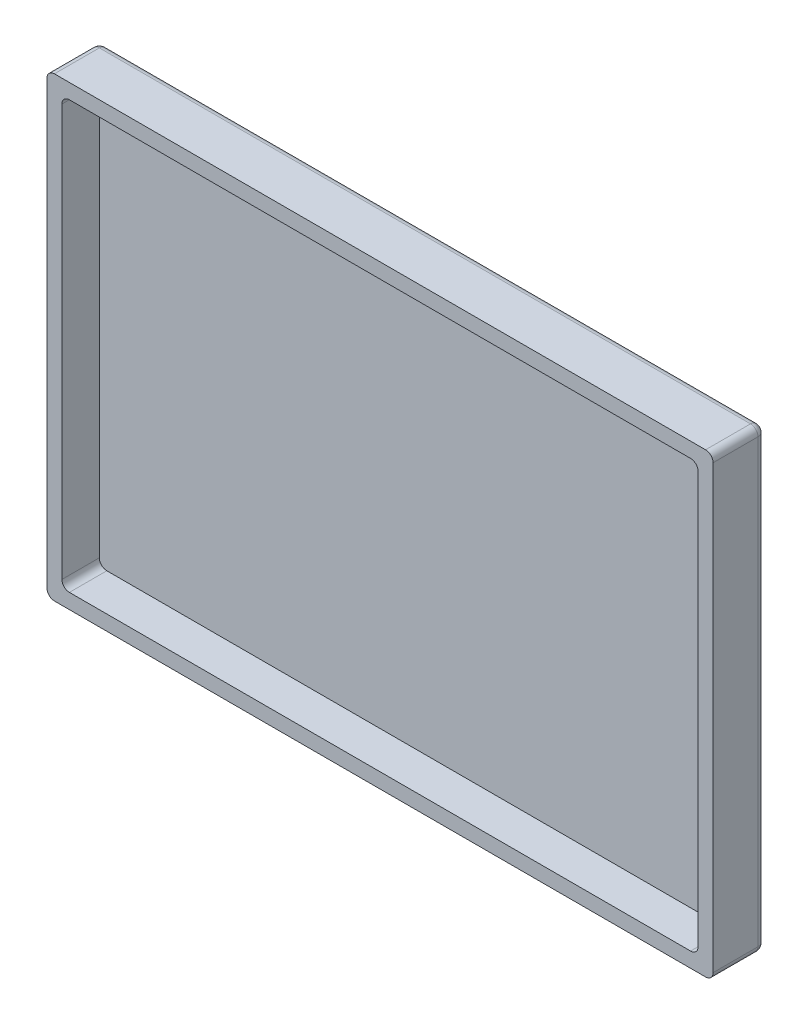
SolidWorks part; units mm, degrees
ref_plane "Plano frontal" through (0, 0, 0) normal (0, 0, 1) x (1, 0, 0)
ref_plane "Plano superior" through (0, 0, 0) normal (0, 1, 0) x (1, 0, 0)
ref_plane "Plano direito" through (0, 0, 0) normal (1, 0, 0) x (0, 0, -1)
sketch "Esboço1" plane through (0, 0, 0) normal (0, 0, 1) x (1, 0, 0)
  line L1 (-44.7633, 12.2986) -> (40.2367, 12.2986)
  line L2 (-44.7633, 12.2986) -> (-44.7633, -44.7014)
  line L3 (-44.7633, -44.7014) -> (40.2367, -44.7014)
  line L4 (40.2367, 12.2986) -> (40.2367, -44.7014)
  line L5 (-46.7633, 14.2986) -> (42.2367, 14.2986)
  line L6 (-46.7633, 14.2986) -> (-46.7633, -46.7014)
  line L7 (-46.7633, -46.7014) -> (42.2367, -46.7014)
  line L8 (42.2367, 14.2986) -> (42.2367, -46.7014)
  dimension "D1" = 57
  dimension "D2" = 85
  dimension "D3" = 2
  dimension "D4" = 2
  dimension "D5" = 2
  dimension "D6" = 2
extrude "Ressalto-extrusão1" add sketch "Esboço1" along normal blind 5
sketch "Esboço2" plane through (0, 0, 0) normal (0, 0, -1) x (-1, 0, 0)
  line L1 (-42.2367, 14.2986) -> (46.7633, 14.2986)
  line L2 (-42.2367, 14.2986) -> (-42.2367, -46.7014)
  line L3 (-42.2367, -46.7014) -> (46.7633, -46.7014)
  line L4 (46.7633, 14.2986) -> (46.7633, -46.7014)
extrude "Ressalto-extrusão2" add sketch "Esboço2" along normal blind 2
fillet "Filete6" radius 1 1 edges at (40.2367, 12.2986, 2.5)
fillet "Filete7" radius 1 3 edges at (-44.7633, 12.2986, 2.5) (-44.7633, -44.7014, 2.5) (40.2367, -44.7014, 2.5)
fillet "Filete10" radius 1 1 edges at (-46.7633, -46.7014, 1.5)
fillet "Filete11" radius 1 3 edges at (42.2367, -46.7014, 1.5) (42.2367, 14.2986, 1.5) (-46.7633, 14.2986, 1.5)
fillet "Filete12" radius 1 8 edges at (-46.4704, 14.0057, -2) (-46.4704, -46.4085, -2) (41.9438, -46.4085, -2) (41.9438, 14.0057, -2) (-46.7633, -16.2014, -2) (-2.2633, -46.7014, -2) (42.2367, -16.2014, -2) (-2.2633, 14.2986, -2)
